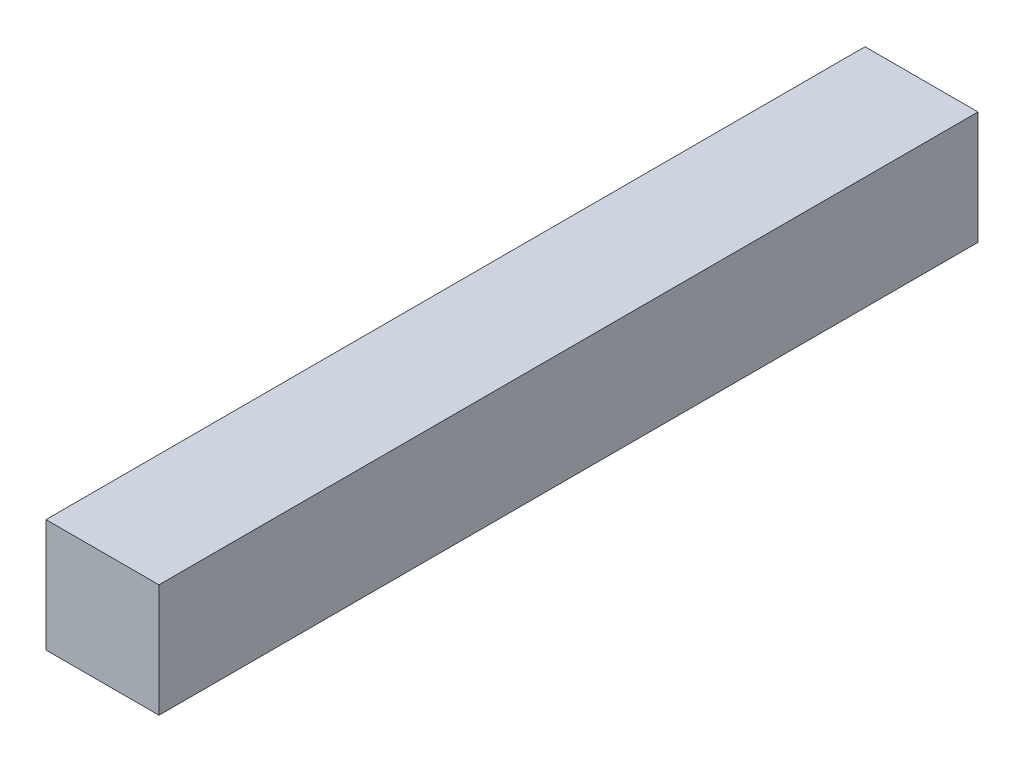
SolidWorks part; units mm, degrees
ref_plane "Front Plane" through (0, 0, 0) normal (0, 0, 1) x (1, 0, 0)
ref_plane "Top Plane" through (0, 0, 0) normal (0, 1, 0) x (1, 0, 0)
ref_plane "Right Plane" through (0, 0, 0) normal (1, 0, 0) x (0, 0, -1)
sketch "Sketch1" plane through (0, 0, 0) normal (0, 1, 0) x (1, 0, 0)
  line L1 (16.6867, 38.2154) -> (36.6867, 38.2154)
  line L2 (16.6867, 38.2154) -> (16.6867, -106.7846)
  line L3 (16.6867, -106.7846) -> (36.6867, -106.7846)
  line L4 (36.6867, 38.2154) -> (36.6867, -106.7846)
  dimension "D1" = 145
  dimension "D2" = 20
extrude "Boss-Extrude1" add sketch "Sketch1" along normal blind 20
